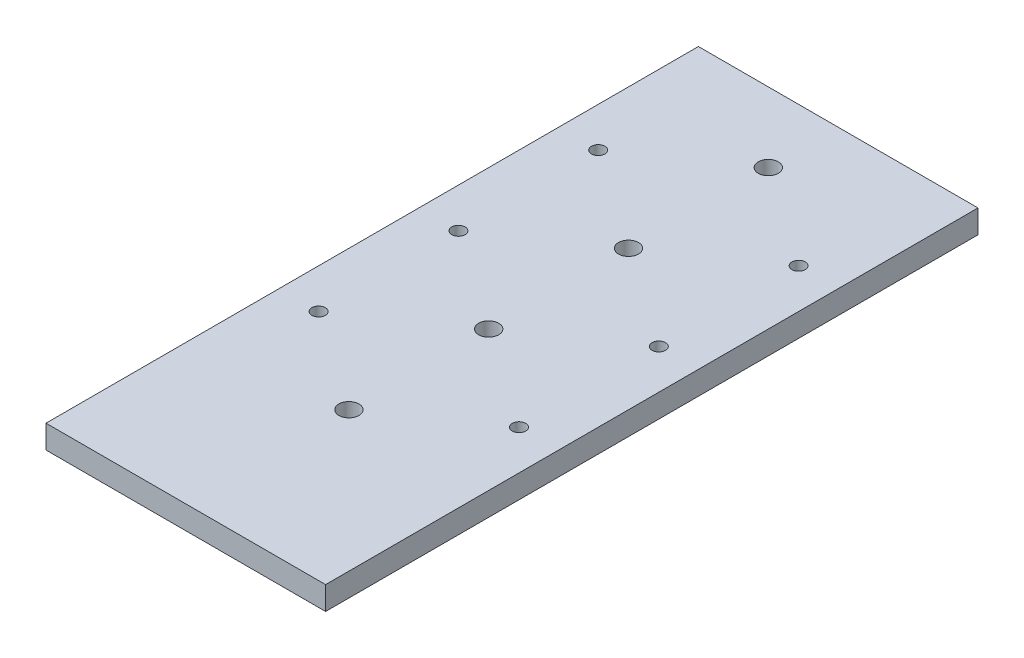
SolidWorks part; units mm, degrees
ref_plane "Front Plane" through (0, 0, 0) normal (0, 0, 1) x (1, 0, 0)
ref_plane "Top Plane" through (0, 0, 0) normal (0, 1, 0) x (1, 0, 0)
ref_plane "Right Plane" through (0, 0, 0) normal (1, 0, 0) x (0, 0, -1)
sketch "Sketch1" plane through (0, 0, 0) normal (0, 1, 0) x (1, 0, 0)
  line L0 (0, 88.9) -> (0, 69.85) construction
  line L1 (-38.1, 88.9) -> (38.1, 88.9)
  line L2 (-38.1, 88.9) -> (-38.1, -88.9)
  line L3 (-38.1, -88.9) -> (38.1, -88.9)
  line L4 (38.1, 88.9) -> (38.1, -88.9)
  line L5 (-38.1, 88.9) -> (38.1, -88.9) construction
  line L6 (-38.1, -88.9) -> (38.1, 88.9) construction
  line L7 (0, 69.85) -> (27.305, 69.85) construction
  line L8 (27.305, 69.85) -> (27.305, 50.8) construction
  circle A0 centre (0, 69.85) radius 2.7305
  circle A1 centre (0, 31.75) radius 2.7305
  circle A2 centre (0, -6.35) radius 2.7305
  circle A3 centre (0, -44.45) radius 2.7305
  circle A4 centre (27.305, 50.8) radius 1.8288
  circle A5 centre (27.305, 12.7) radius 1.8288
  circle A6 centre (27.305, -25.4) radius 1.8288
  circle A7 centre (-27.305, 12.7) radius 1.8288
  circle A8 centre (-27.305, -25.4) radius 1.8288
  circle A9 centre (-27.305, 50.8) radius 1.8288
  point P0 (0, 0)
  dimension "D4" = 5.461
  dimension "D10" = 3.6576
  dimension "D1" = 76.2
  dimension "D2" = 177.8
  dimension "D3" = 19.05
  dimension "D6" = 27.305
  dimension "D7" = 19.05
  dimension "D5" = 4
  dimension "D8" = 3
  dimension "D9" = 2
extrude "Boss-Extrude1" add sketch "Sketch1" against normal blind 6.35
